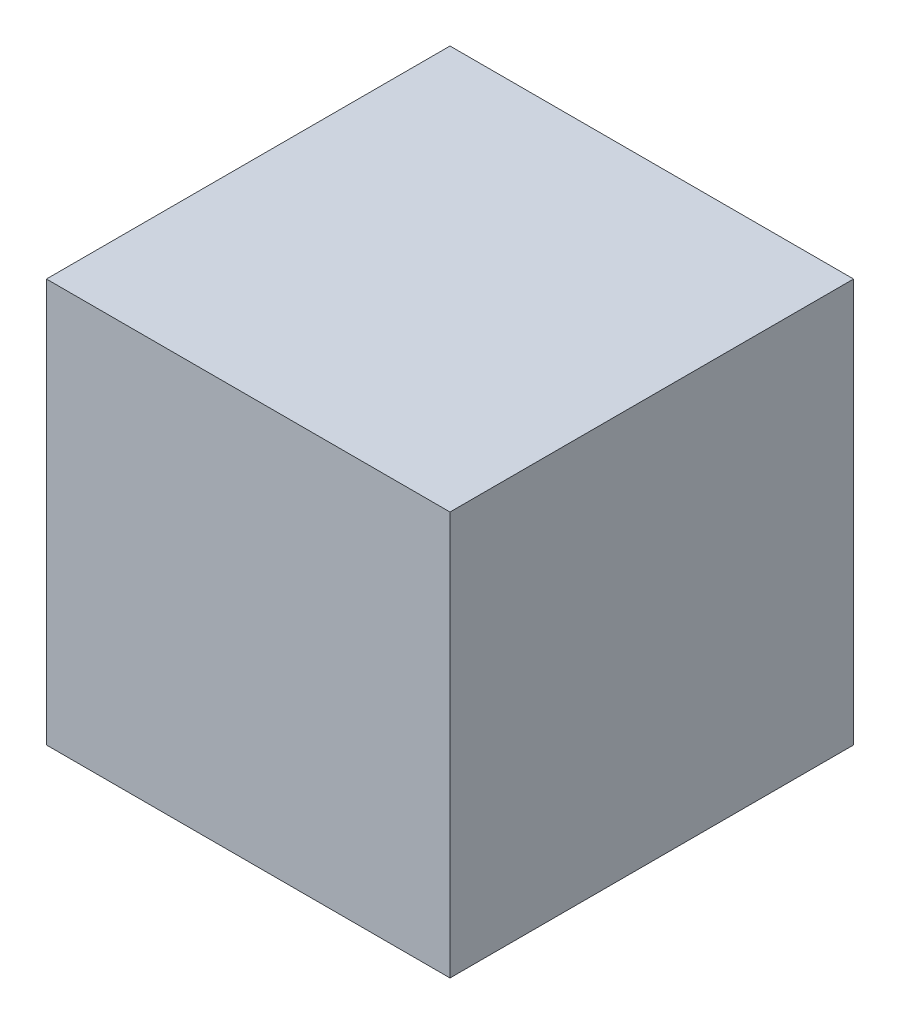
SolidWorks part; units mm, degrees
ref_plane "Front Plane" through (0, 0, 0) normal (0, 0, 1) x (1, 0, 0)
ref_plane "Top Plane" through (0, 0, 0) normal (0, 1, 0) x (1, 0, 0)
ref_plane "Right Plane" through (0, 0, 0) normal (1, 0, 0) x (0, 0, -1)
sketch "Sketch1" plane through (0, 0, 0) normal (0, 0, 1) x (1, 0, 0)
  line L1 (-34.0126, 23.0809) -> (15.9874, 23.0809)
  line L2 (-34.0126, 23.0809) -> (-34.0126, -26.9191)
  line L3 (-34.0126, -26.9191) -> (15.9874, -26.9191)
  line L4 (15.9874, 23.0809) -> (15.9874, -26.9191)
  dimension "D1" = 50
  dimension "D2" = 50
extrude "Boss-Extrude1" add sketch "Sketch1" along normal blind 50
